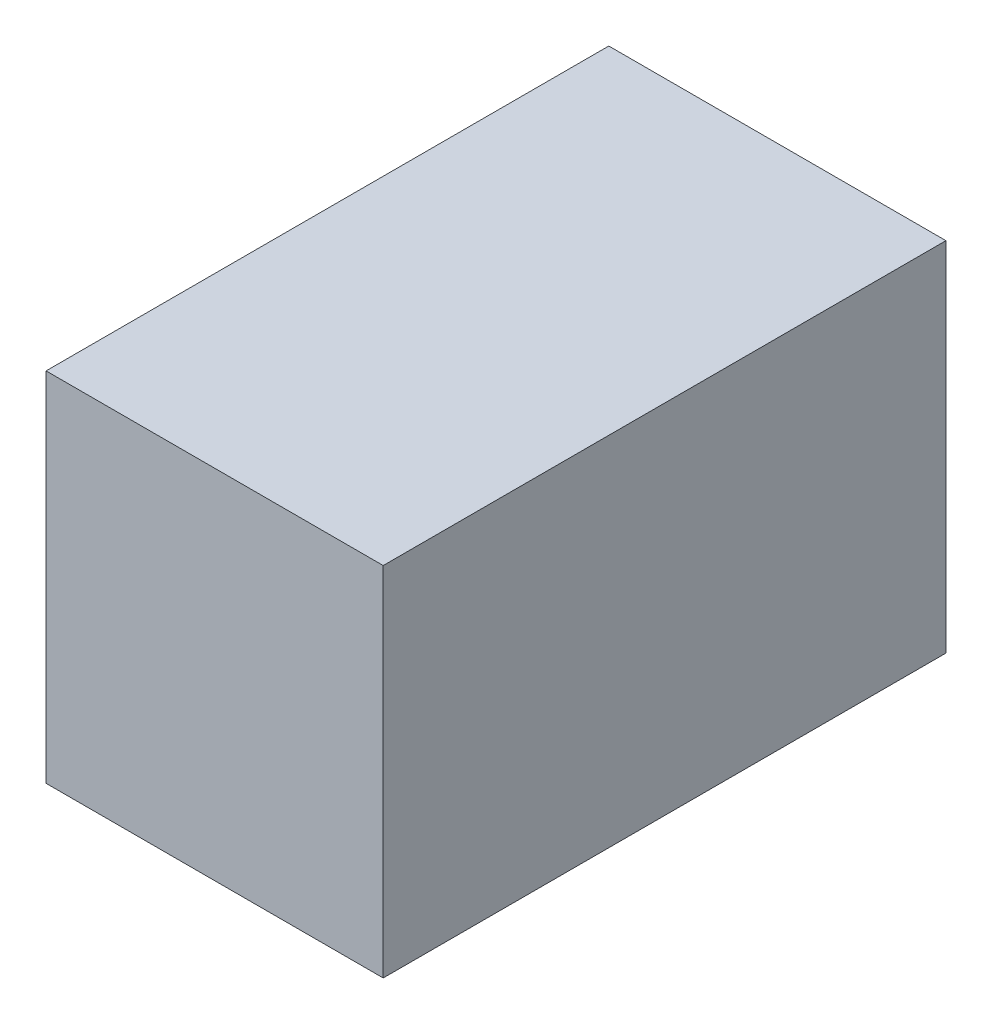
SolidWorks part; units mm, degrees
ref_plane "Front Plane" through (0, 0, 0) normal (0, 0, 1) x (1, 0, 0)
ref_plane "Top Plane" through (0, 0, 0) normal (0, 1, 0) x (1, 0, 0)
ref_plane "Right Plane" through (0, 0, 0) normal (1, 0, 0) x (0, 0, -1)
sketch "Sketch4" plane through (0, 0, 0) normal (1, 0, 0) x (0, 0, -1)
  line L1 (-15.525, 9.125) -> (15.525, 9.125)
  line L2 (-15.525, 9.125) -> (-15.525, -9.125)
  line L3 (-15.525, -9.125) -> (15.525, -9.125)
  line L4 (15.525, 9.125) -> (15.525, -9.125)
  line L5 (-15.525, 9.125) -> (15.525, -9.125) construction
  line L6 (-15.525, -9.125) -> (15.525, 9.125) construction
  point P0 (0, 0)
  dimension "D1" = 31.05
  dimension "D2" = 18.25
extrude "Boss-Extrude1" add sketch "Sketch4" along normal blind 19
shell "Shell1" thickness 2
sketch "Sketch5" plane through (0, 0, -17.525) normal (0, 0, -1) x (-1, 0, 0)
  line L0 (0, -11.125) -> (0, 11.125) construction
  line L1 (0, 9.125) -> (-12, 9.125)
  line L2 (-12, 9.125) -> (-12, -9.125)
  line L3 (-12, -9.125) -> (0, -9.125)
  line L4 (-21, 11.125) -> (0, 11.125) construction
  line L5 (-21, -11.125) -> (0, -11.125) construction
  line L6 (0, 9.125) -> (0, -9.125)
  dimension "D1" = 12
  dimension "D2" = 2
  dimension "D3" = 2
extrude "Cut-Extrude1" cut sketch "Sketch5" against normal up to surface (2 mm away) up to face at (9.5, 0, -15.525)
equation "\"terminalRad\"= 3mm"
equation "\"terminalLen\"= 10.5mm"
equation "\"threadlen\"=11"
